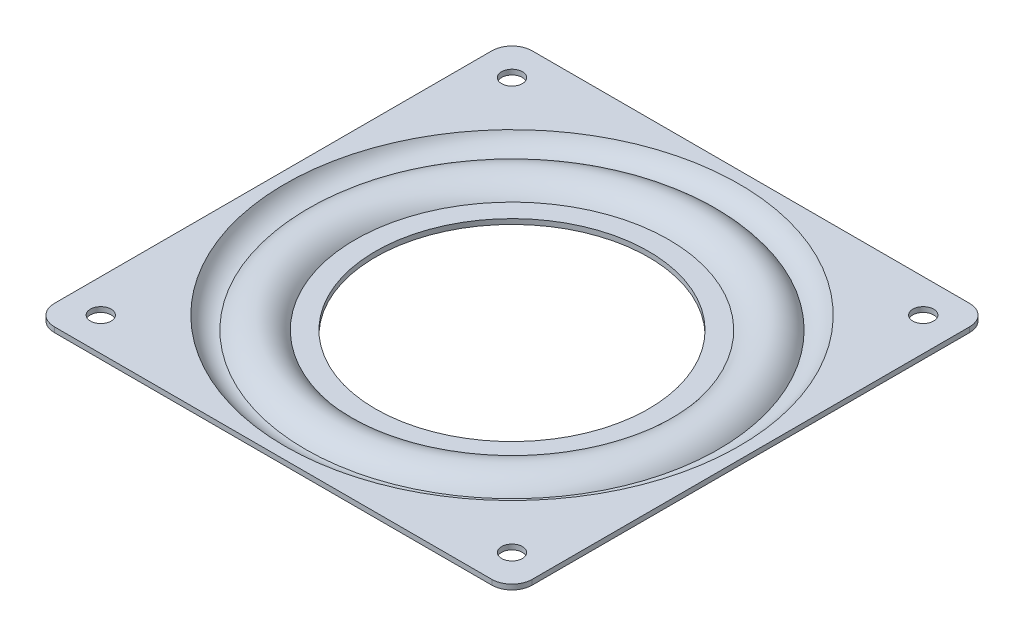
SolidWorks part; units mm, degrees
ref_plane "前视基准面" through (0, 0, 0) normal (0, 0, 1) x (1, 0, 0)
ref_plane "上视基准面" through (0, 0, 0) normal (0, 1, 0) x (1, 0, 0)
ref_plane "右视基准面" through (0, 0, 0) normal (1, 0, 0) x (0, 0, -1)
sketch "草图1" plane through (0, 0, 0) normal (0, 0, 1) x (1, 0, 0)
  line L0 (-36.7805, 0) -> (-35.9228, 0)
  line L1 (0, 6.9172) -> (0, -6.9172) construction
  line L2 (-31, -2.5698) -> (-27, -2.5698)
  line L3 (-35.9228, 0) -> (0, 0) construction
  line L4 (0, 0) -> (43.3864, 0) construction
  line L5 (-43.3864, 0) -> (-36.7805, 0) construction
  line L6 (-31.5531, -3.5698) -> (-27, -3.5698)
  line L7 (-27, -2.5698) -> (-27, -3.5698)
  line L8 (-44.9105, 0) -> (-45.8139, -0.4289)
  arc A0 (-44.9105, 0) -> (-40.8455, -2.5698) centre (-40.8455, 1.9302) ccw
  arc A1 (-40.8455, -2.5698) -> (-31, -2.5698) centre (-35.9228, -6) cw
  arc A2 (-40.8455, -2.5698) -> (-36.8127, -0.0664) centre (-40.8455, 1.9302) ccw construction
  arc A3 (-36.8127, -0.0664) -> (-36.7805, 0) centre (-40.8455, 1.9302) ccw
  arc A4 (-45.8139, -0.4289) -> (-40.2759, -3.5402) centre (-40.8455, 1.9302) ccw
  arc A5 (-40.2759, -3.5402) -> (-31.5531, -3.5698) centre (-35.9228, -6) cw
  point P4 (0, 0)
  point P8 (0, 0)
  dimension "D1" = 4.5
  dimension "D2" = 6
  dimension "D3" = 27
  dimension "D4" = 4
revolve "旋转1" add sketch "草图1" angle 360 about L1
sketch "草图2" plane through (0, 0, 0) normal (0, 1, 0) x (1, 0, 0)
  line L0 (0, 0) -> (-40.6586, 40.6586) construction
  line L1 (-43.25, 47.25) -> (47.25, 47.25)
  line L2 (-47.25, 43.25) -> (-47.25, -47.25)
  line L3 (-47.25, -47.25) -> (47.25, -47.25)
  line L4 (47.25, 47.25) -> (47.25, -47.25)
  line L5 (-47.25, 47.25) -> (47.25, -47.25) construction
  line L6 (-47.25, -47.25) -> (47.25, 47.25) construction
  line L7 (0, 0) -> (40.6586, 40.6586) construction
  line L8 (0, 0) -> (-43.25, 43.25) construction
  circle A0 centre (0, 0) radius 44.9105 construction
  circle A1 centre (0, 0) radius 44.9105
  arc A2 (-43.25, 47.25) -> (-47.25, 43.25) centre (-43.25, 43.25) ccw
  circle A3 centre (-40.6586, 40.6586) radius 2.05
  circle A4 centre (40.6586, 40.6586) radius 2.05
  circle A5 centre (40.6586, -40.6586) radius 2.05
  circle A6 centre (-40.6586, -40.6586) radius 2.05
  arc A7 (47.25, 43.25) -> (43.25, 47.25) centre (43.25, 43.25) ccw
  arc A8 (43.25, -47.25) -> (47.25, -43.25) centre (43.25, -43.25) ccw
  arc A9 (-47.25, -43.25) -> (-43.25, -47.25) centre (-43.25, -43.25) ccw
  point P12 (42.5591, 54.1613)
  point P14 (0.2209, 0.2209)
  point P15 (117.6078, 44.198)
  dimension "D3" = 4
  dimension "D4" = 4.1
  dimension "D9" = 4
  dimension "D1" = 94.5
  dimension "D2" = 94.5
  dimension "D5" = 57.5
  dimension "D7" = 90
  dimension "D8" = 57.5
  dimension "D10" = 61.1647
  dimension "D6" = 4
extrude "凸台-拉伸1" add sketch "草图2" against normal blind 1 contours L2 A9 L3 A8 L4 A7 L1 A2 A6 A5 A4 A3 A1
